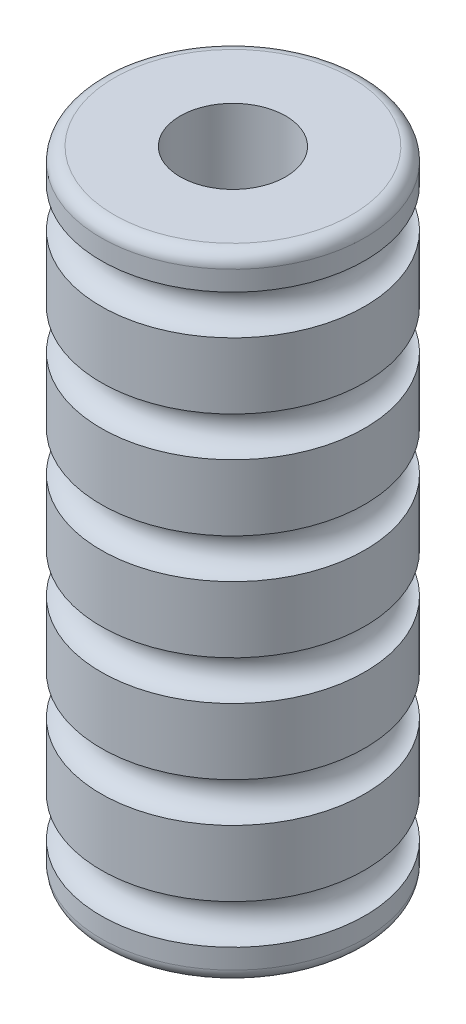
SolidWorks part; units mm, degrees
ref_plane "Front" through (0, 0, 0) normal (0, 0, 1) x (1, 0, 0)
ref_plane "Top" through (0, 0, 0) normal (0, 1, 0) x (1, 0, 0)
ref_plane "Right" through (0, 0, 0) normal (1, 0, 0) x (0, 0, -1)
sketch "Sketch1" plane through (0, 0, 0) normal (1, 0, 0) x (0, 0, -1)
  line L0 (31.75, 144.4625) -> (31.75, 149.225)
  line L1 (0, 0) -> (28.575, 0)
  line L2 (0, 0) -> (0, 152.4)
  line L3 (0, 152.4) -> (28.575, 152.4)
  line L4 (31.75, 3.175) -> (31.75, 7.9375)
  line L5 (31.75, 119.0625) -> (31.75, 134.9375)
  line L6 (31.75, 93.6625) -> (31.75, 109.5375)
  line L7 (31.75, 68.2625) -> (31.75, 84.1375)
  line L8 (31.75, 42.8625) -> (31.75, 58.7375)
  line L9 (31.75, 17.4625) -> (31.75, 33.3375)
  arc A0 (31.75, 17.4625) -> (31.75, 7.9375) centre (31.75, 12.7) ccw
  arc A1 (31.75, 42.8625) -> (31.75, 33.3375) centre (31.75, 38.1) ccw
  arc A2 (31.75, 68.2625) -> (31.75, 58.7375) centre (31.75, 63.5) ccw
  arc A3 (31.75, 93.6625) -> (31.75, 84.1375) centre (31.75, 88.9) ccw
  arc A4 (31.75, 119.0625) -> (31.75, 109.5375) centre (31.75, 114.3) ccw
  arc A5 (31.75, 144.4625) -> (31.75, 134.9375) centre (31.75, 139.7) ccw
  arc A6 (28.575, 0) -> (31.75, 3.175) centre (28.575, 3.175) ccw
  arc A7 (28.575, 152.4) -> (31.75, 149.225) centre (28.575, 149.225) cw
  point P25 (31.75, 0)
  dimension "D3" = 9.525
  dimension "D6" = 3.175
  dimension "D1" = 12.7
  dimension "D2" = 31.75
  dimension "D4" = 12.7
  dimension "D5" = 6
revolve "Revolve1" add sketch "Sketch1" angle 360 about L2
sketch "Sketch2" plane through (0, 0, 0) normal (0, -1, 0) x (1, 0, 0)
  circle A0 centre (0, 0) radius 12.7
  dimension "D1" = 25.4
extrude "Cut-Extrude1" cut sketch "Sketch2" against normal up to next
